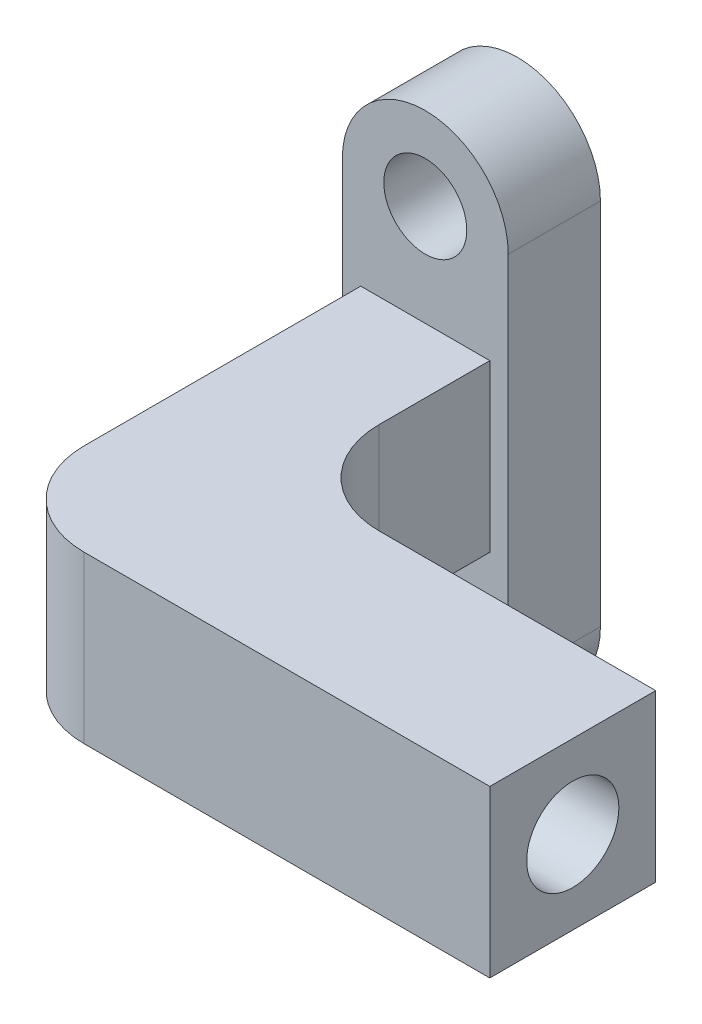
SolidWorks part; units mm, degrees
ref_plane "Front Plane" through (0, 0, 0) normal (0, 0, 1) x (1, 0, 0)
ref_plane "Top Plane" through (0, 0, 0) normal (0, 1, 0) x (1, 0, 0)
ref_plane "Right Plane" through (0, 0, 0) normal (1, 0, 0) x (0, 0, -1)
sketch "Sketch1" plane through (0, 0, 0) normal (0, 0, 1) x (1, 0, 0)
  line L0 (4.5, 10) -> (4.5, -10)
  line L1 (-4.5, 10) -> (-4.5, -10)
  circle A0 centre (0, 10) radius 2.25
  circle A1 centre (0, -10) radius 2.25
  circle A2 centre (0, 10) radius 4.5
  circle A3 centre (0, -10) radius 4.5
  dimension "D1" = 4.5
  dimension "D2" = 9
  dimension "D3" = 4.5
  dimension "D4" = 9
  dimension "D5" = 20
  dimension "D6" = 10
extrude "Boss-Extrude1" add sketch "Sketch1" along normal blind 5 contours A3 L0 A2 L1 | A3 A1 | A0
sketch "Sketch2" plane through (0, 0, 5) normal (0, 0, 1) x (1, 0, 0)
  line L1 (-3.5, -4.5) -> (3.5, -4.5)
  line L2 (-3.5, -4.5) -> (-3.5, 4.5)
  line L3 (-3.5, 4.5) -> (3.5, 4.5)
  line L4 (3.5, -4.5) -> (3.5, 4.5)
  line L5 (-3.5, -4.5) -> (3.5, 4.5) construction
  line L6 (-3.5, 4.5) -> (3.5, -4.5) construction
  point P0 (0, 0)
  dimension "D1" = 9
  dimension "D2" = 7
extrude "Boss-Extrude2" add sketch "Sketch2" along normal blind 20
sketch "Sketch4" plane through (3.5, 0, 0) normal (1, 0, 0) x (0, 0, -1)
  line L0 (-25, -4.5) -> (-5, -4.5) construction
  line L1 (-25, 4.5) -> (-16, 4.5)
  line L2 (-25, 4.5) -> (-25, -4.5)
  line L3 (-25, -4.5) -> (-16, -4.5)
  line L4 (-16, 4.5) -> (-16, -4.5)
  dimension "D1" = 9
extrude "Boss-Extrude4" add sketch "Sketch4" along normal blind 20
sketch "Sketch5" plane through (23.5, 0, 0) normal (1, 0, 0) x (0, 0, -1)
  circle A0 centre (-20.5, 0) radius 2.5
  dimension "D1" = 5
extrude "Cut-Extrude1" cut sketch "Sketch5" against normal blind 25
fillet "Fillet1" radius 5 1 edges at (3.5, 0, 16)
fillet "Fillet2" radius 5 1 edges at (-3.5, 0, 25)
